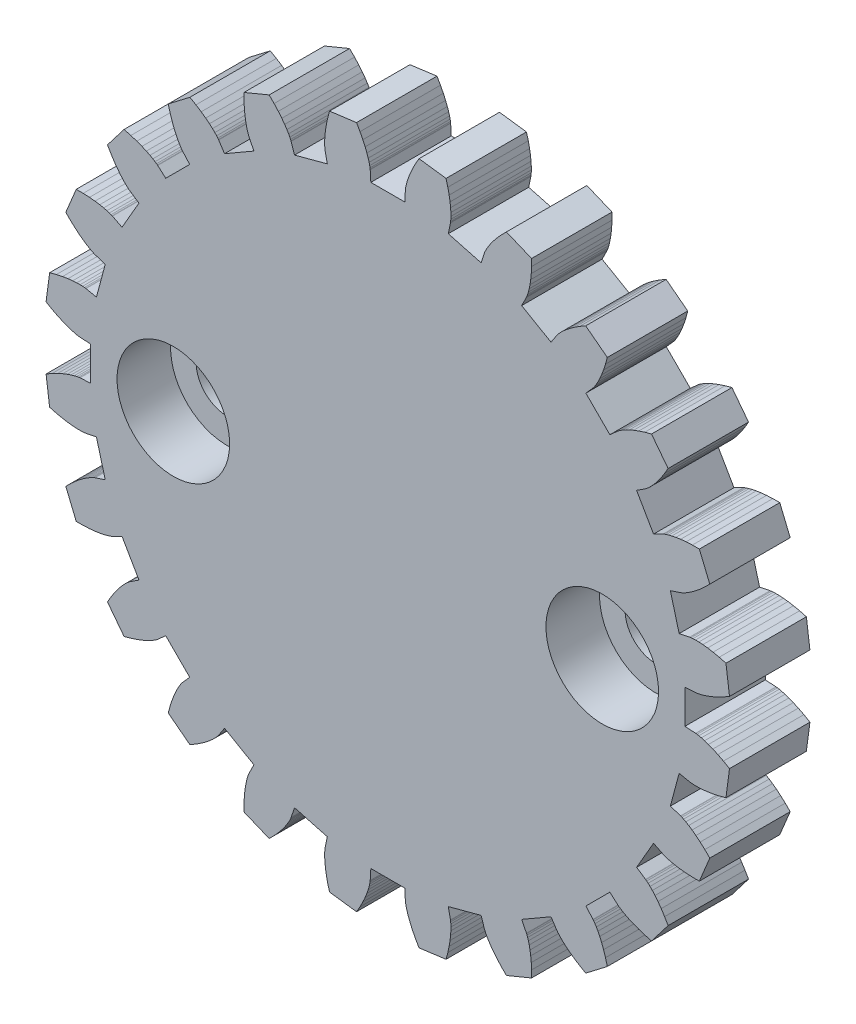
SolidWorks part; units mm, degrees
material "ABS"
ref_plane "Front Plane" through (0, 0, 0) normal (0, 0, 1) x (1, 0, 0)
ref_plane "Top Plane" through (0, 0, 0) normal (0, 1, 0) x (1, 0, 0)
ref_plane "Right Plane" through (0, 0, 0) normal (1, 0, 0) x (0, 0, -1)
sketch "Model" plane through (0, 0, 0) normal (0, 0, 1) x (1, 0, 0)
  line L0 (11.4813, -0.6559) -> (11.0819, -0.6331)
  line L1 (11.0819, -0.6331) -> (11.0819, 0.6331)
  line L2 (11.4813, 0.6559) -> (11.0819, 0.6331)
  line L3 (11.4813, 0.6559) -> (11.495, 0.6571)
  line L4 (11.495, 0.6571) -> (11.5358, 0.6626)
  line L5 (11.5358, 0.6626) -> (11.6033, 0.6749)
  line L6 (11.6033, 0.6749) -> (11.697, 0.6968)
  line L7 (11.697, 0.6968) -> (11.8158, 0.7307)
  line L8 (11.8158, 0.7307) -> (11.9589, 0.7792)
  line L9 (11.9589, 0.7792) -> (12.125, 0.8446)
  line L10 (12.125, 0.8446) -> (12.3128, 0.9294)
  line L11 (12.3128, 0.9294) -> (12.5206, 1.0358)
  line L12 (12.5206, 1.0358) -> (12.7468, 1.1658)
  line L13 (11.2598, 2.338) -> (11.2734, 2.3404)
  line L14 (11.2734, 2.3404) -> (11.3142, 2.3457)
  line L15 (11.3142, 2.3457) -> (11.3827, 2.3512)
  line L16 (11.3827, 2.3512) -> (11.4787, 2.3543)
  line L17 (11.4787, 2.3543) -> (11.6023, 2.3524)
  line L18 (11.6023, 2.3524) -> (11.7531, 2.3426)
  line L19 (11.7531, 2.3426) -> (11.9305, 2.3223)
  line L20 (11.9305, 2.3223) -> (12.1338, 2.289)
  line L21 (12.1338, 2.289) -> (12.362, 2.2401)
  line L22 (12.362, 2.2401) -> (12.6142, 2.173)
  line L23 (12.7468, 1.1658) -> (12.6142, 2.173)
  line L24 (11.2598, 2.338) -> (10.8682, 2.2567)
  line L25 (10.8682, 2.2567) -> (10.5405, 3.4797)
  line L26 (10.9203, 3.6051) -> (10.5405, 3.4797)
  line L27 (10.9203, 3.6051) -> (10.9332, 3.6098)
  line L28 (10.9332, 3.6098) -> (10.9712, 3.6257)
  line L29 (10.9712, 3.6257) -> (11.0333, 3.6551)
  line L30 (11.0333, 3.6551) -> (11.1181, 3.7004)
  line L31 (11.1181, 3.7004) -> (11.2241, 3.764)
  line L32 (11.2241, 3.764) -> (11.3497, 3.8478)
  line L33 (11.3497, 3.8478) -> (11.4933, 3.954)
  line L34 (11.4933, 3.954) -> (11.6527, 4.0845)
  line L35 (11.6527, 4.0845) -> (11.8259, 4.241)
  line L36 (11.8259, 4.241) -> (12.0107, 4.4252)
  line L37 (10.271, 5.1726) -> (10.2835, 5.1784)
  line L38 (10.2835, 5.1784) -> (10.3216, 5.1941)
  line L39 (10.3216, 5.1941) -> (10.3863, 5.2172)
  line L40 (10.3863, 5.2172) -> (10.4783, 5.245)
  line L41 (10.4783, 5.245) -> (10.5981, 5.2751)
  line L42 (10.5981, 5.2751) -> (10.7463, 5.3047)
  line L43 (10.7463, 5.3047) -> (10.9229, 5.331)
  line L44 (10.9229, 5.331) -> (11.1279, 5.3515)
  line L45 (11.1279, 5.3515) -> (11.361, 5.3633)
  line L46 (11.361, 5.3633) -> (11.622, 5.3638)
  line L47 (12.0107, 4.4252) -> (11.622, 5.3638)
  line L48 (10.271, 5.1726) -> (9.9138, 4.9927)
  line L49 (9.9138, 4.9927) -> (9.2807, 6.0892)
  line L50 (9.6151, 6.3087) -> (9.2807, 6.0892)
  line L51 (9.6151, 6.3087) -> (9.6264, 6.3166)
  line L52 (9.6264, 6.3166) -> (9.659, 6.3417)
  line L53 (9.659, 6.3417) -> (9.7113, 6.3862)
  line L54 (9.7113, 6.3862) -> (9.7815, 6.4519)
  line L55 (9.7815, 6.4519) -> (9.8675, 6.5407)
  line L56 (9.8675, 6.5407) -> (9.9671, 6.6542)
  line L57 (9.9671, 6.6542) -> (10.0783, 6.794)
  line L58 (10.0783, 6.794) -> (10.1985, 6.9613)
  line L59 (10.1985, 6.9613) -> (10.3253, 7.1573)
  line L60 (10.3253, 7.1573) -> (10.4561, 7.383)
  line L61 (8.5823, 7.6547) -> (8.5928, 7.6635)
  line L62 (8.5928, 7.6635) -> (8.6256, 7.6885)
  line L63 (8.6256, 7.6885) -> (8.6821, 7.7275)
  line L64 (8.6821, 7.7275) -> (8.7637, 7.7783)
  line L65 (8.7637, 7.7783) -> (8.8717, 7.8384)
  line L66 (8.8717, 7.8384) -> (9.0072, 7.9053)
  line L67 (9.0072, 7.9053) -> (9.1709, 7.9764)
  line L68 (9.1709, 7.9764) -> (9.3636, 8.0492)
  line L69 (9.3636, 8.0492) -> (9.5858, 8.121)
  line L70 (9.5858, 8.121) -> (9.8377, 8.189)
  line L71 (10.4561, 7.383) -> (9.8377, 8.189)
  line L72 (8.5823, 7.6547) -> (8.2838, 7.3885)
  line L73 (8.2838, 7.3885) -> (7.3885, 8.2838)
  line L74 (7.6547, 8.5823) -> (7.3885, 8.2838)
  line L75 (7.6547, 8.5823) -> (7.6635, 8.5928)
  line L76 (7.6635, 8.5928) -> (7.6885, 8.6256)
  line L77 (7.6885, 8.6256) -> (7.7275, 8.6821)
  line L78 (7.7275, 8.6821) -> (7.7783, 8.7637)
  line L79 (7.7783, 8.7637) -> (7.8384, 8.8717)
  line L80 (7.8384, 8.8717) -> (7.9053, 9.0072)
  line L81 (7.9053, 9.0072) -> (7.9764, 9.1709)
  line L82 (7.9764, 9.1709) -> (8.0492, 9.3636)
  line L83 (8.0492, 9.3636) -> (8.121, 9.5858)
  line L84 (8.121, 9.5858) -> (8.189, 9.8377)
  line L85 (6.3087, 9.6151) -> (6.3166, 9.6264)
  line L86 (6.3166, 9.6264) -> (6.3417, 9.659)
  line L87 (6.3417, 9.659) -> (6.3862, 9.7113)
  line L88 (6.3862, 9.7113) -> (6.4519, 9.7815)
  line L89 (6.4519, 9.7815) -> (6.5407, 9.8675)
  line L90 (6.5407, 9.8675) -> (6.6542, 9.9671)
  line L91 (6.6542, 9.9671) -> (6.794, 10.0783)
  line L92 (6.794, 10.0783) -> (6.9613, 10.1985)
  line L93 (6.9613, 10.1985) -> (7.1573, 10.3253)
  line L94 (7.1573, 10.3253) -> (7.383, 10.4561)
  line L95 (8.189, 9.8377) -> (7.383, 10.4561)
  line L96 (6.3087, 9.6151) -> (6.0892, 9.2807)
  line L97 (6.0892, 9.2807) -> (4.9927, 9.9138)
  line L98 (5.1726, 10.271) -> (4.9927, 9.9138)
  line L99 (5.1726, 10.271) -> (5.1784, 10.2835)
  line L100 (5.1784, 10.2835) -> (5.1941, 10.3216)
  line L101 (5.1941, 10.3216) -> (5.2172, 10.3863)
  line L102 (5.2172, 10.3863) -> (5.245, 10.4783)
  line L103 (5.245, 10.4783) -> (5.2751, 10.5981)
  line L104 (5.2751, 10.5981) -> (5.3047, 10.7463)
  line L105 (5.3047, 10.7463) -> (5.331, 10.9229)
  line L106 (5.331, 10.9229) -> (5.3515, 11.1279)
  line L107 (5.3515, 11.1279) -> (5.3633, 11.361)
  line L108 (5.3633, 11.361) -> (5.3638, 11.622)
  line L109 (3.6051, 10.9203) -> (3.6098, 10.9332)
  line L110 (3.6098, 10.9332) -> (3.6257, 10.9712)
  line L111 (3.6257, 10.9712) -> (3.6551, 11.0333)
  line L112 (3.6551, 11.0333) -> (3.7004, 11.1181)
  line L113 (3.7004, 11.1181) -> (3.764, 11.2241)
  line L114 (3.764, 11.2241) -> (3.8478, 11.3497)
  line L115 (3.8478, 11.3497) -> (3.954, 11.4933)
  line L116 (3.954, 11.4933) -> (4.0845, 11.6527)
  line L117 (4.0845, 11.6527) -> (4.241, 11.8259)
  line L118 (4.241, 11.8259) -> (4.4252, 12.0107)
  line L119 (5.3638, 11.622) -> (4.4252, 12.0107)
  line L120 (3.6051, 10.9203) -> (3.4797, 10.5405)
  line L121 (3.4797, 10.5405) -> (2.2567, 10.8682)
  line L122 (2.338, 11.2598) -> (2.2567, 10.8682)
  line L123 (2.338, 11.2598) -> (2.3404, 11.2734)
  line L124 (2.3404, 11.2734) -> (2.3457, 11.3142)
  line L125 (2.3457, 11.3142) -> (2.3512, 11.3827)
  line L126 (2.3512, 11.3827) -> (2.3543, 11.4787)
  line L127 (2.3543, 11.4787) -> (2.3524, 11.6023)
  line L128 (2.3524, 11.6023) -> (2.3426, 11.7531)
  line L129 (2.3426, 11.7531) -> (2.3223, 11.9305)
  line L130 (2.3223, 11.9305) -> (2.289, 12.1338)
  line L131 (2.289, 12.1338) -> (2.2401, 12.362)
  line L132 (2.2401, 12.362) -> (2.173, 12.6142)
  line L133 (0.6559, 11.4813) -> (0.6571, 11.495)
  line L134 (0.6571, 11.495) -> (0.6626, 11.5358)
  line L135 (0.6626, 11.5358) -> (0.6749, 11.6033)
  line L136 (0.6749, 11.6033) -> (0.6968, 11.697)
  line L137 (0.6968, 11.697) -> (0.7307, 11.8158)
  line L138 (0.7307, 11.8158) -> (0.7792, 11.9589)
  line L139 (0.7792, 11.9589) -> (0.8446, 12.125)
  line L140 (0.8446, 12.125) -> (0.9294, 12.3128)
  line L141 (0.9294, 12.3128) -> (1.0358, 12.5206)
  line L142 (1.0358, 12.5206) -> (1.1658, 12.7468)
  line L143 (2.173, 12.6142) -> (1.1658, 12.7468)
  line L144 (0.6559, 11.4813) -> (0.6331, 11.0819)
  line L145 (0.6331, 11.0819) -> (-0.6331, 11.0819)
  line L146 (-0.6559, 11.4813) -> (-0.6331, 11.0819)
  line L147 (-0.6559, 11.4813) -> (-0.6571, 11.495)
  line L148 (-0.6571, 11.495) -> (-0.6626, 11.5358)
  line L149 (-0.6626, 11.5358) -> (-0.6749, 11.6033)
  line L150 (-0.6749, 11.6033) -> (-0.6968, 11.697)
  line L151 (-0.6968, 11.697) -> (-0.7307, 11.8158)
  line L152 (-0.7307, 11.8158) -> (-0.7792, 11.9589)
  line L153 (-0.7792, 11.9589) -> (-0.8446, 12.125)
  line L154 (-0.8446, 12.125) -> (-0.9294, 12.3128)
  line L155 (-0.9294, 12.3128) -> (-1.0358, 12.5206)
  line L156 (-1.0358, 12.5206) -> (-1.1658, 12.7468)
  line L157 (-2.338, 11.2598) -> (-2.3404, 11.2734)
  line L158 (-2.3404, 11.2734) -> (-2.3457, 11.3142)
  line L159 (-2.3457, 11.3142) -> (-2.3512, 11.3827)
  line L160 (-2.3512, 11.3827) -> (-2.3543, 11.4787)
  line L161 (-2.3543, 11.4787) -> (-2.3524, 11.6023)
  line L162 (-2.3524, 11.6023) -> (-2.3426, 11.7531)
  line L163 (-2.3426, 11.7531) -> (-2.3223, 11.9305)
  line L164 (-2.3223, 11.9305) -> (-2.289, 12.1338)
  line L165 (-2.289, 12.1338) -> (-2.2401, 12.362)
  line L166 (-2.2401, 12.362) -> (-2.173, 12.6142)
  line L167 (-1.1658, 12.7468) -> (-2.173, 12.6142)
  line L168 (-2.338, 11.2598) -> (-2.2567, 10.8682)
  line L169 (-2.2567, 10.8682) -> (-3.4797, 10.5405)
  line L170 (-3.6051, 10.9203) -> (-3.4797, 10.5405)
  line L171 (-3.6051, 10.9203) -> (-3.6098, 10.9332)
  line L172 (-3.6098, 10.9332) -> (-3.6257, 10.9712)
  line L173 (-3.6257, 10.9712) -> (-3.6551, 11.0333)
  line L174 (-3.6551, 11.0333) -> (-3.7004, 11.1181)
  line L175 (-3.7004, 11.1181) -> (-3.764, 11.2241)
  line L176 (-3.764, 11.2241) -> (-3.8478, 11.3497)
  line L177 (-3.8478, 11.3497) -> (-3.954, 11.4933)
  line L178 (-3.954, 11.4933) -> (-4.0845, 11.6527)
  line L179 (-4.0845, 11.6527) -> (-4.241, 11.8259)
  line L180 (-4.241, 11.8259) -> (-4.4252, 12.0107)
  line L181 (-5.1726, 10.271) -> (-5.1784, 10.2835)
  line L182 (-5.1784, 10.2835) -> (-5.1941, 10.3216)
  line L183 (-5.1941, 10.3216) -> (-5.2172, 10.3863)
  line L184 (-5.2172, 10.3863) -> (-5.245, 10.4783)
  line L185 (-5.245, 10.4783) -> (-5.2751, 10.5981)
  line L186 (-5.2751, 10.5981) -> (-5.3047, 10.7463)
  line L187 (-5.3047, 10.7463) -> (-5.331, 10.9229)
  line L188 (-5.331, 10.9229) -> (-5.3515, 11.1279)
  line L189 (-5.3515, 11.1279) -> (-5.3633, 11.361)
  line L190 (-5.3633, 11.361) -> (-5.3638, 11.622)
  line L191 (-4.4252, 12.0107) -> (-5.3638, 11.622)
  line L192 (-5.1726, 10.271) -> (-4.9927, 9.9138)
  line L193 (-4.9927, 9.9138) -> (-6.0892, 9.2807)
  line L194 (-6.3087, 9.6151) -> (-6.0892, 9.2807)
  line L195 (-6.3087, 9.6151) -> (-6.3166, 9.6264)
  line L196 (-6.3166, 9.6264) -> (-6.3417, 9.659)
  line L197 (-6.3417, 9.659) -> (-6.3862, 9.7113)
  line L198 (-6.3862, 9.7113) -> (-6.4519, 9.7815)
  line L199 (-6.4519, 9.7815) -> (-6.5407, 9.8675)
  line L200 (-6.5407, 9.8675) -> (-6.6542, 9.9671)
  line L201 (-6.6542, 9.9671) -> (-6.794, 10.0783)
  line L202 (-6.794, 10.0783) -> (-6.9613, 10.1985)
  line L203 (-6.9613, 10.1985) -> (-7.1573, 10.3253)
  line L204 (-7.1573, 10.3253) -> (-7.383, 10.4561)
  line L205 (-7.6547, 8.5823) -> (-7.6635, 8.5928)
  line L206 (-7.6635, 8.5928) -> (-7.6885, 8.6256)
  line L207 (-7.6885, 8.6256) -> (-7.7275, 8.6821)
  line L208 (-7.7275, 8.6821) -> (-7.7783, 8.7637)
  line L209 (-7.7783, 8.7637) -> (-7.8384, 8.8717)
  line L210 (-7.8384, 8.8717) -> (-7.9053, 9.0072)
  line L211 (-7.9053, 9.0072) -> (-7.9764, 9.1709)
  line L212 (-7.9764, 9.1709) -> (-8.0492, 9.3636)
  line L213 (-8.0492, 9.3636) -> (-8.121, 9.5858)
  line L214 (-8.121, 9.5858) -> (-8.189, 9.8377)
  line L215 (-7.383, 10.4561) -> (-8.189, 9.8377)
  line L216 (-7.6547, 8.5823) -> (-7.3885, 8.2838)
  line L217 (-7.3885, 8.2838) -> (-8.2838, 7.3885)
  line L218 (-8.5823, 7.6547) -> (-8.2838, 7.3885)
  line L219 (-8.5823, 7.6547) -> (-8.5928, 7.6635)
  line L220 (-8.5928, 7.6635) -> (-8.6256, 7.6885)
  line L221 (-8.6256, 7.6885) -> (-8.6821, 7.7275)
  line L222 (-8.6821, 7.7275) -> (-8.7637, 7.7783)
  line L223 (-8.7637, 7.7783) -> (-8.8717, 7.8384)
  line L224 (-8.8717, 7.8384) -> (-9.0072, 7.9053)
  line L225 (-9.0072, 7.9053) -> (-9.1709, 7.9764)
  line L226 (-9.1709, 7.9764) -> (-9.3636, 8.0492)
  line L227 (-9.3636, 8.0492) -> (-9.5858, 8.121)
  line L228 (-9.5858, 8.121) -> (-9.8377, 8.189)
  line L229 (-9.6151, 6.3087) -> (-9.6264, 6.3166)
  line L230 (-9.6264, 6.3166) -> (-9.659, 6.3417)
  line L231 (-9.659, 6.3417) -> (-9.7113, 6.3862)
  line L232 (-9.7113, 6.3862) -> (-9.7815, 6.4519)
  line L233 (-9.7815, 6.4519) -> (-9.8675, 6.5407)
  line L234 (-9.8675, 6.5407) -> (-9.9671, 6.6542)
  line L235 (-9.9671, 6.6542) -> (-10.0783, 6.794)
  line L236 (-10.0783, 6.794) -> (-10.1985, 6.9613)
  line L237 (-10.1985, 6.9613) -> (-10.3253, 7.1573)
  line L238 (-10.3253, 7.1573) -> (-10.4561, 7.383)
  line L239 (-9.8377, 8.189) -> (-10.4561, 7.383)
  line L240 (-9.6151, 6.3087) -> (-9.2807, 6.0892)
  line L241 (-9.2807, 6.0892) -> (-9.9138, 4.9927)
  line L242 (-10.271, 5.1726) -> (-9.9138, 4.9927)
  line L243 (-10.271, 5.1726) -> (-10.2835, 5.1784)
  line L244 (-10.2835, 5.1784) -> (-10.3216, 5.1941)
  line L245 (-10.3216, 5.1941) -> (-10.3863, 5.2172)
  line L246 (-10.3863, 5.2172) -> (-10.4783, 5.245)
  line L247 (-10.4783, 5.245) -> (-10.5981, 5.2751)
  line L248 (-10.5981, 5.2751) -> (-10.7463, 5.3047)
  line L249 (-10.7463, 5.3047) -> (-10.9229, 5.331)
  line L250 (-10.9229, 5.331) -> (-11.1279, 5.3515)
  line L251 (-11.1279, 5.3515) -> (-11.361, 5.3633)
  line L252 (-11.361, 5.3633) -> (-11.622, 5.3638)
  line L253 (-10.9203, 3.6051) -> (-10.9332, 3.6098)
  line L254 (-10.9332, 3.6098) -> (-10.9712, 3.6257)
  line L255 (-10.9712, 3.6257) -> (-11.0333, 3.6551)
  line L256 (-11.0333, 3.6551) -> (-11.1181, 3.7004)
  line L257 (-11.1181, 3.7004) -> (-11.2241, 3.764)
  line L258 (-11.2241, 3.764) -> (-11.3497, 3.8478)
  line L259 (-11.3497, 3.8478) -> (-11.4933, 3.954)
  line L260 (-11.4933, 3.954) -> (-11.6527, 4.0845)
  line L261 (-11.6527, 4.0845) -> (-11.8259, 4.241)
  line L262 (-11.8259, 4.241) -> (-12.0107, 4.4252)
  line L263 (-11.622, 5.3638) -> (-12.0107, 4.4252)
  line L264 (-10.9203, 3.6051) -> (-10.5405, 3.4797)
  line L265 (-10.5405, 3.4797) -> (-10.8682, 2.2567)
  line L266 (-11.2598, 2.338) -> (-10.8682, 2.2567)
  line L267 (-11.2598, 2.338) -> (-11.2734, 2.3404)
  line L268 (-11.2734, 2.3404) -> (-11.3142, 2.3457)
  line L269 (-11.3142, 2.3457) -> (-11.3827, 2.3512)
  line L270 (-11.3827, 2.3512) -> (-11.4787, 2.3543)
  line L271 (-11.4787, 2.3543) -> (-11.6023, 2.3524)
  line L272 (-11.6023, 2.3524) -> (-11.7531, 2.3426)
  line L273 (-11.7531, 2.3426) -> (-11.9305, 2.3223)
  line L274 (-11.9305, 2.3223) -> (-12.1338, 2.289)
  line L275 (-12.1338, 2.289) -> (-12.362, 2.2401)
  line L276 (-12.362, 2.2401) -> (-12.6142, 2.173)
  line L277 (-11.4813, 0.6559) -> (-11.495, 0.6571)
  line L278 (-11.495, 0.6571) -> (-11.5358, 0.6626)
  line L279 (-11.5358, 0.6626) -> (-11.6033, 0.6749)
  line L280 (-11.6033, 0.6749) -> (-11.697, 0.6968)
  line L281 (-11.697, 0.6968) -> (-11.8158, 0.7307)
  line L282 (-11.8158, 0.7307) -> (-11.9589, 0.7792)
  line L283 (-11.9589, 0.7792) -> (-12.125, 0.8446)
  line L284 (-12.125, 0.8446) -> (-12.3128, 0.9294)
  line L285 (-12.3128, 0.9294) -> (-12.5206, 1.0358)
  line L286 (-12.5206, 1.0358) -> (-12.7468, 1.1658)
  line L287 (-12.6142, 2.173) -> (-12.7468, 1.1658)
  line L288 (-11.4813, 0.6559) -> (-11.0819, 0.6331)
  line L289 (-11.0819, 0.6331) -> (-11.0819, -0.6331)
  line L290 (-11.4813, -0.6559) -> (-11.0819, -0.6331)
  line L291 (-11.4813, -0.6559) -> (-11.495, -0.6571)
  line L292 (-11.495, -0.6571) -> (-11.5358, -0.6626)
  line L293 (-11.5358, -0.6626) -> (-11.6033, -0.6749)
  line L294 (-11.6033, -0.6749) -> (-11.697, -0.6968)
  line L295 (-11.697, -0.6968) -> (-11.8158, -0.7307)
  line L296 (-11.8158, -0.7307) -> (-11.9589, -0.7792)
  line L297 (-11.9589, -0.7792) -> (-12.125, -0.8446)
  line L298 (-12.125, -0.8446) -> (-12.3128, -0.9294)
  line L299 (-12.3128, -0.9294) -> (-12.5206, -1.0358)
  line L300 (-12.5206, -1.0358) -> (-12.7468, -1.1658)
  line L301 (-11.2598, -2.338) -> (-11.2734, -2.3404)
  line L302 (-11.2734, -2.3404) -> (-11.3142, -2.3457)
  line L303 (-11.3142, -2.3457) -> (-11.3827, -2.3512)
  line L304 (-11.3827, -2.3512) -> (-11.4787, -2.3543)
  line L305 (-11.4787, -2.3543) -> (-11.6023, -2.3524)
  line L306 (-11.6023, -2.3524) -> (-11.7531, -2.3426)
  line L307 (-11.7531, -2.3426) -> (-11.9305, -2.3223)
  line L308 (-11.9305, -2.3223) -> (-12.1338, -2.289)
  line L309 (-12.1338, -2.289) -> (-12.362, -2.2401)
  line L310 (-12.362, -2.2401) -> (-12.6142, -2.173)
  line L311 (-12.7468, -1.1658) -> (-12.6142, -2.173)
  line L312 (-11.2598, -2.338) -> (-10.8682, -2.2567)
  line L313 (-10.8682, -2.2567) -> (-10.5405, -3.4797)
  line L314 (-10.9203, -3.6051) -> (-10.5405, -3.4797)
  line L315 (-10.9203, -3.6051) -> (-10.9332, -3.6098)
  line L316 (-10.9332, -3.6098) -> (-10.9712, -3.6257)
  line L317 (-10.9712, -3.6257) -> (-11.0333, -3.6551)
  line L318 (-11.0333, -3.6551) -> (-11.1181, -3.7004)
  line L319 (-11.1181, -3.7004) -> (-11.2241, -3.764)
  line L320 (-11.2241, -3.764) -> (-11.3497, -3.8478)
  line L321 (-11.3497, -3.8478) -> (-11.4933, -3.954)
  line L322 (-11.4933, -3.954) -> (-11.6527, -4.0845)
  line L323 (-11.6527, -4.0845) -> (-11.8259, -4.241)
  line L324 (-11.8259, -4.241) -> (-12.0107, -4.4252)
  line L325 (-10.271, -5.1726) -> (-10.2835, -5.1784)
  line L326 (-10.2835, -5.1784) -> (-10.3216, -5.1941)
  line L327 (-10.3216, -5.1941) -> (-10.3863, -5.2172)
  line L328 (-10.3863, -5.2172) -> (-10.4783, -5.245)
  line L329 (-10.4783, -5.245) -> (-10.5981, -5.2751)
  line L330 (-10.5981, -5.2751) -> (-10.7463, -5.3047)
  line L331 (-10.7463, -5.3047) -> (-10.9229, -5.331)
  line L332 (-10.9229, -5.331) -> (-11.1279, -5.3515)
  line L333 (-11.1279, -5.3515) -> (-11.361, -5.3633)
  line L334 (-11.361, -5.3633) -> (-11.622, -5.3638)
  line L335 (-12.0107, -4.4252) -> (-11.622, -5.3638)
  line L336 (-10.271, -5.1726) -> (-9.9138, -4.9927)
  line L337 (-9.9138, -4.9927) -> (-9.2807, -6.0892)
  line L338 (-9.6151, -6.3087) -> (-9.2807, -6.0892)
  line L339 (-9.6151, -6.3087) -> (-9.6264, -6.3166)
  line L340 (-9.6264, -6.3166) -> (-9.659, -6.3417)
  line L341 (-9.659, -6.3417) -> (-9.7113, -6.3862)
  line L342 (-9.7113, -6.3862) -> (-9.7815, -6.4519)
  line L343 (-9.7815, -6.4519) -> (-9.8675, -6.5407)
  line L344 (-9.8675, -6.5407) -> (-9.9671, -6.6542)
  line L345 (-9.9671, -6.6542) -> (-10.0783, -6.794)
  line L346 (-10.0783, -6.794) -> (-10.1985, -6.9613)
  line L347 (-10.1985, -6.9613) -> (-10.3253, -7.1573)
  line L348 (-10.3253, -7.1573) -> (-10.4561, -7.383)
  line L349 (-8.5823, -7.6547) -> (-8.5928, -7.6635)
  line L350 (-8.5928, -7.6635) -> (-8.6256, -7.6885)
  line L351 (-8.6256, -7.6885) -> (-8.6821, -7.7275)
  line L352 (-8.6821, -7.7275) -> (-8.7637, -7.7783)
  line L353 (-8.7637, -7.7783) -> (-8.8717, -7.8384)
  line L354 (-8.8717, -7.8384) -> (-9.0072, -7.9053)
  line L355 (-9.0072, -7.9053) -> (-9.1709, -7.9764)
  line L356 (-9.1709, -7.9764) -> (-9.3636, -8.0492)
  line L357 (-9.3636, -8.0492) -> (-9.5858, -8.121)
  line L358 (-9.5858, -8.121) -> (-9.8377, -8.189)
  line L359 (-10.4561, -7.383) -> (-9.8377, -8.189)
  line L360 (-8.5823, -7.6547) -> (-8.2838, -7.3885)
  line L361 (-8.2838, -7.3885) -> (-7.3885, -8.2838)
  line L362 (-7.6547, -8.5823) -> (-7.3885, -8.2838)
  line L363 (-7.6547, -8.5823) -> (-7.6635, -8.5928)
  line L364 (-7.6635, -8.5928) -> (-7.6885, -8.6256)
  line L365 (-7.6885, -8.6256) -> (-7.7275, -8.6821)
  line L366 (-7.7275, -8.6821) -> (-7.7783, -8.7637)
  line L367 (-7.7783, -8.7637) -> (-7.8384, -8.8717)
  line L368 (-7.8384, -8.8717) -> (-7.9053, -9.0072)
  line L369 (-7.9053, -9.0072) -> (-7.9764, -9.1709)
  line L370 (-7.9764, -9.1709) -> (-8.0492, -9.3636)
  line L371 (-8.0492, -9.3636) -> (-8.121, -9.5858)
  line L372 (-8.121, -9.5858) -> (-8.189, -9.8377)
  line L373 (-6.3087, -9.6151) -> (-6.3166, -9.6264)
  line L374 (-6.3166, -9.6264) -> (-6.3417, -9.659)
  line L375 (-6.3417, -9.659) -> (-6.3862, -9.7113)
  line L376 (-6.3862, -9.7113) -> (-6.4519, -9.7815)
  line L377 (-6.4519, -9.7815) -> (-6.5407, -9.8675)
  line L378 (-6.5407, -9.8675) -> (-6.6542, -9.9671)
  line L379 (-6.6542, -9.9671) -> (-6.794, -10.0783)
  line L380 (-6.794, -10.0783) -> (-6.9613, -10.1985)
  line L381 (-6.9613, -10.1985) -> (-7.1573, -10.3253)
  line L382 (-7.1573, -10.3253) -> (-7.383, -10.4561)
  line L383 (-8.189, -9.8377) -> (-7.383, -10.4561)
  line L384 (-6.3087, -9.6151) -> (-6.0892, -9.2807)
  line L385 (-6.0892, -9.2807) -> (-4.9927, -9.9138)
  line L386 (-5.1726, -10.271) -> (-4.9927, -9.9138)
  line L387 (-5.1726, -10.271) -> (-5.1784, -10.2835)
  line L388 (-5.1784, -10.2835) -> (-5.1941, -10.3216)
  line L389 (-5.1941, -10.3216) -> (-5.2172, -10.3863)
  line L390 (-5.2172, -10.3863) -> (-5.245, -10.4783)
  line L391 (-5.245, -10.4783) -> (-5.2751, -10.5981)
  line L392 (-5.2751, -10.5981) -> (-5.3047, -10.7463)
  line L393 (-5.3047, -10.7463) -> (-5.331, -10.9229)
  line L394 (-5.331, -10.9229) -> (-5.3515, -11.1279)
  line L395 (-5.3515, -11.1279) -> (-5.3633, -11.361)
  line L396 (-5.3633, -11.361) -> (-5.3638, -11.622)
  line L397 (-3.6051, -10.9203) -> (-3.6098, -10.9332)
  line L398 (-3.6098, -10.9332) -> (-3.6257, -10.9712)
  line L399 (-3.6257, -10.9712) -> (-3.6551, -11.0333)
  line L400 (-3.6551, -11.0333) -> (-3.7004, -11.1181)
  line L401 (-3.7004, -11.1181) -> (-3.764, -11.2241)
  line L402 (-3.764, -11.2241) -> (-3.8478, -11.3497)
  line L403 (-3.8478, -11.3497) -> (-3.954, -11.4933)
  line L404 (-3.954, -11.4933) -> (-4.0845, -11.6527)
  line L405 (-4.0845, -11.6527) -> (-4.241, -11.8259)
  line L406 (-4.241, -11.8259) -> (-4.4252, -12.0107)
  line L407 (-5.3638, -11.622) -> (-4.4252, -12.0107)
  line L408 (-3.6051, -10.9203) -> (-3.4797, -10.5405)
  line L409 (-3.4797, -10.5405) -> (-2.2567, -10.8682)
  line L410 (-2.338, -11.2598) -> (-2.2567, -10.8682)
  line L411 (-2.338, -11.2598) -> (-2.3404, -11.2734)
  line L412 (-2.3404, -11.2734) -> (-2.3457, -11.3142)
  line L413 (-2.3457, -11.3142) -> (-2.3512, -11.3827)
  line L414 (-2.3512, -11.3827) -> (-2.3543, -11.4787)
  line L415 (-2.3543, -11.4787) -> (-2.3524, -11.6023)
  line L416 (-2.3524, -11.6023) -> (-2.3426, -11.7531)
  line L417 (-2.3426, -11.7531) -> (-2.3223, -11.9305)
  line L418 (-2.3223, -11.9305) -> (-2.289, -12.1338)
  line L419 (-2.289, -12.1338) -> (-2.2401, -12.362)
  line L420 (-2.2401, -12.362) -> (-2.173, -12.6142)
  line L421 (-0.6559, -11.4813) -> (-0.6571, -11.495)
  line L422 (-0.6571, -11.495) -> (-0.6626, -11.5358)
  line L423 (-0.6626, -11.5358) -> (-0.6749, -11.6033)
  line L424 (-0.6749, -11.6033) -> (-0.6968, -11.697)
  line L425 (-0.6968, -11.697) -> (-0.7307, -11.8158)
  line L426 (-0.7307, -11.8158) -> (-0.7792, -11.9589)
  line L427 (-0.7792, -11.9589) -> (-0.8446, -12.125)
  line L428 (-0.8446, -12.125) -> (-0.9294, -12.3128)
  line L429 (-0.9294, -12.3128) -> (-1.0358, -12.5206)
  line L430 (-1.0358, -12.5206) -> (-1.1658, -12.7468)
  line L431 (-2.173, -12.6142) -> (-1.1658, -12.7468)
  line L432 (-0.6559, -11.4813) -> (-0.6331, -11.0819)
  line L433 (-0.6331, -11.0819) -> (0.6331, -11.0819)
  line L434 (0.6559, -11.4813) -> (0.6331, -11.0819)
  line L435 (0.6559, -11.4813) -> (0.6571, -11.495)
  line L436 (0.6571, -11.495) -> (0.6626, -11.5358)
  line L437 (0.6626, -11.5358) -> (0.6749, -11.6033)
  line L438 (0.6749, -11.6033) -> (0.6968, -11.697)
  line L439 (0.6968, -11.697) -> (0.7307, -11.8158)
  line L440 (0.7307, -11.8158) -> (0.7792, -11.9589)
  line L441 (0.7792, -11.9589) -> (0.8446, -12.125)
  line L442 (0.8446, -12.125) -> (0.9294, -12.3128)
  line L443 (0.9294, -12.3128) -> (1.0358, -12.5206)
  line L444 (1.0358, -12.5206) -> (1.1658, -12.7468)
  line L445 (2.338, -11.2598) -> (2.3404, -11.2734)
  line L446 (2.3404, -11.2734) -> (2.3457, -11.3142)
  line L447 (2.3457, -11.3142) -> (2.3512, -11.3827)
  line L448 (2.3512, -11.3827) -> (2.3543, -11.4787)
  line L449 (2.3543, -11.4787) -> (2.3524, -11.6023)
  line L450 (2.3524, -11.6023) -> (2.3426, -11.7531)
  line L451 (2.3426, -11.7531) -> (2.3223, -11.9305)
  line L452 (2.3223, -11.9305) -> (2.289, -12.1338)
  line L453 (2.289, -12.1338) -> (2.2401, -12.362)
  line L454 (2.2401, -12.362) -> (2.173, -12.6142)
  line L455 (1.1658, -12.7468) -> (2.173, -12.6142)
  line L456 (2.338, -11.2598) -> (2.2567, -10.8682)
  line L457 (2.2567, -10.8682) -> (3.4797, -10.5405)
  line L458 (3.6051, -10.9203) -> (3.4797, -10.5405)
  line L459 (3.6051, -10.9203) -> (3.6098, -10.9332)
  line L460 (3.6098, -10.9332) -> (3.6257, -10.9712)
  line L461 (3.6257, -10.9712) -> (3.6551, -11.0333)
  line L462 (3.6551, -11.0333) -> (3.7004, -11.1181)
  line L463 (3.7004, -11.1181) -> (3.764, -11.2241)
  line L464 (3.764, -11.2241) -> (3.8478, -11.3497)
  line L465 (3.8478, -11.3497) -> (3.954, -11.4933)
  line L466 (3.954, -11.4933) -> (4.0845, -11.6527)
  line L467 (4.0845, -11.6527) -> (4.241, -11.8259)
  line L468 (4.241, -11.8259) -> (4.4252, -12.0107)
  line L469 (5.1726, -10.271) -> (5.1784, -10.2835)
  line L470 (5.1784, -10.2835) -> (5.1941, -10.3216)
  line L471 (5.1941, -10.3216) -> (5.2172, -10.3863)
  line L472 (5.2172, -10.3863) -> (5.245, -10.4783)
  line L473 (5.245, -10.4783) -> (5.2751, -10.5981)
  line L474 (5.2751, -10.5981) -> (5.3047, -10.7463)
  line L475 (5.3047, -10.7463) -> (5.331, -10.9229)
  line L476 (5.331, -10.9229) -> (5.3515, -11.1279)
  line L477 (5.3515, -11.1279) -> (5.3633, -11.361)
  line L478 (5.3633, -11.361) -> (5.3638, -11.622)
  line L479 (4.4252, -12.0107) -> (5.3638, -11.622)
  line L480 (5.1726, -10.271) -> (4.9927, -9.9138)
  line L481 (4.9927, -9.9138) -> (6.0892, -9.2807)
  line L482 (6.3087, -9.6151) -> (6.0892, -9.2807)
  line L483 (6.3087, -9.6151) -> (6.3166, -9.6264)
  line L484 (6.3166, -9.6264) -> (6.3417, -9.659)
  line L485 (6.3417, -9.659) -> (6.3862, -9.7113)
  line L486 (6.3862, -9.7113) -> (6.4519, -9.7815)
  line L487 (6.4519, -9.7815) -> (6.5407, -9.8675)
  line L488 (6.5407, -9.8675) -> (6.6542, -9.9671)
  line L489 (6.6542, -9.9671) -> (6.794, -10.0783)
  line L490 (6.794, -10.0783) -> (6.9613, -10.1985)
  line L491 (6.9613, -10.1985) -> (7.1573, -10.3253)
  line L492 (7.1573, -10.3253) -> (7.383, -10.4561)
  line L493 (7.6547, -8.5823) -> (7.6635, -8.5928)
  line L494 (7.6635, -8.5928) -> (7.6885, -8.6256)
  line L495 (7.6885, -8.6256) -> (7.7275, -8.6821)
  line L496 (7.7275, -8.6821) -> (7.7783, -8.7637)
  line L497 (7.7783, -8.7637) -> (7.8384, -8.8717)
  line L498 (7.8384, -8.8717) -> (7.9053, -9.0072)
  line L499 (7.9053, -9.0072) -> (7.9764, -9.1709)
  line L500 (7.9764, -9.1709) -> (8.0492, -9.3636)
  line L501 (8.0492, -9.3636) -> (8.121, -9.5858)
  line L502 (8.121, -9.5858) -> (8.189, -9.8377)
  line L503 (7.383, -10.4561) -> (8.189, -9.8377)
  line L504 (7.6547, -8.5823) -> (7.3885, -8.2838)
  line L505 (7.3885, -8.2838) -> (8.2838, -7.3885)
  line L506 (8.5823, -7.6547) -> (8.2838, -7.3885)
  line L507 (8.5823, -7.6547) -> (8.5928, -7.6635)
  line L508 (8.5928, -7.6635) -> (8.6256, -7.6885)
  line L509 (8.6256, -7.6885) -> (8.6821, -7.7275)
  line L510 (8.6821, -7.7275) -> (8.7637, -7.7783)
  line L511 (8.7637, -7.7783) -> (8.8717, -7.8384)
  line L512 (8.8717, -7.8384) -> (9.0072, -7.9053)
  line L513 (9.0072, -7.9053) -> (9.1709, -7.9764)
  line L514 (9.1709, -7.9764) -> (9.3636, -8.0492)
  line L515 (9.3636, -8.0492) -> (9.5858, -8.121)
  line L516 (9.5858, -8.121) -> (9.8377, -8.189)
  line L517 (9.6151, -6.3087) -> (9.6264, -6.3166)
  line L518 (9.6264, -6.3166) -> (9.659, -6.3417)
  line L519 (9.659, -6.3417) -> (9.7113, -6.3862)
  line L520 (9.7113, -6.3862) -> (9.7815, -6.4519)
  line L521 (9.7815, -6.4519) -> (9.8675, -6.5407)
  line L522 (9.8675, -6.5407) -> (9.9671, -6.6542)
  line L523 (9.9671, -6.6542) -> (10.0783, -6.794)
  line L524 (10.0783, -6.794) -> (10.1985, -6.9613)
  line L525 (10.1985, -6.9613) -> (10.3253, -7.1573)
  line L526 (10.3253, -7.1573) -> (10.4561, -7.383)
  line L527 (9.8377, -8.189) -> (10.4561, -7.383)
  line L528 (9.6151, -6.3087) -> (9.2807, -6.0892)
  line L529 (9.2807, -6.0892) -> (9.9138, -4.9927)
  line L530 (10.271, -5.1726) -> (9.9138, -4.9927)
  line L531 (10.271, -5.1726) -> (10.2835, -5.1784)
  line L532 (10.2835, -5.1784) -> (10.3216, -5.1941)
  line L533 (10.3216, -5.1941) -> (10.3863, -5.2172)
  line L534 (10.3863, -5.2172) -> (10.4783, -5.245)
  line L535 (10.4783, -5.245) -> (10.5981, -5.2751)
  line L536 (10.5981, -5.2751) -> (10.7463, -5.3047)
  line L537 (10.7463, -5.3047) -> (10.9229, -5.331)
  line L538 (10.9229, -5.331) -> (11.1279, -5.3515)
  line L539 (11.1279, -5.3515) -> (11.361, -5.3633)
  line L540 (11.361, -5.3633) -> (11.622, -5.3638)
  line L541 (10.9203, -3.6051) -> (10.9332, -3.6098)
  line L542 (10.9332, -3.6098) -> (10.9712, -3.6257)
  line L543 (10.9712, -3.6257) -> (11.0333, -3.6551)
  line L544 (11.0333, -3.6551) -> (11.1181, -3.7004)
  line L545 (11.1181, -3.7004) -> (11.2241, -3.764)
  line L546 (11.2241, -3.764) -> (11.3497, -3.8478)
  line L547 (11.3497, -3.8478) -> (11.4933, -3.954)
  line L548 (11.4933, -3.954) -> (11.6527, -4.0845)
  line L549 (11.6527, -4.0845) -> (11.8259, -4.241)
  line L550 (11.8259, -4.241) -> (12.0107, -4.4252)
  line L551 (11.622, -5.3638) -> (12.0107, -4.4252)
  line L552 (10.9203, -3.6051) -> (10.5405, -3.4797)
  line L553 (10.5405, -3.4797) -> (10.8682, -2.2567)
  line L554 (11.2598, -2.338) -> (10.8682, -2.2567)
  line L555 (11.2598, -2.338) -> (11.2734, -2.3404)
  line L556 (11.2734, -2.3404) -> (11.3142, -2.3457)
  line L557 (11.3142, -2.3457) -> (11.3827, -2.3512)
  line L558 (11.3827, -2.3512) -> (11.4787, -2.3543)
  line L559 (11.4787, -2.3543) -> (11.6023, -2.3524)
  line L560 (11.6023, -2.3524) -> (11.7531, -2.3426)
  line L561 (11.7531, -2.3426) -> (11.9305, -2.3223)
  line L562 (11.9305, -2.3223) -> (12.1338, -2.289)
  line L563 (12.1338, -2.289) -> (12.362, -2.2401)
  line L564 (12.362, -2.2401) -> (12.6142, -2.173)
  line L565 (11.4813, -0.6559) -> (11.495, -0.6571)
  line L566 (11.495, -0.6571) -> (11.5358, -0.6626)
  line L567 (11.5358, -0.6626) -> (11.6033, -0.6749)
  line L568 (11.6033, -0.6749) -> (11.697, -0.6968)
  line L569 (11.697, -0.6968) -> (11.8158, -0.7307)
  line L570 (11.8158, -0.7307) -> (11.9589, -0.7792)
  line L571 (11.9589, -0.7792) -> (12.125, -0.8446)
  line L572 (12.125, -0.8446) -> (12.3128, -0.9294)
  line L573 (12.3128, -0.9294) -> (12.5206, -1.0358)
  line L574 (12.5206, -1.0358) -> (12.7468, -1.1658)
  line L575 (12.6142, -2.173) -> (12.7468, -1.1658)
extrude "Main Gear Body" add sketch "Model" along normal blind 3
sketch "Sketch1" plane through (0, 0, 3) normal (0, 0, 1) x (1, 0, 0)
  line L0 (-8, 0) -> (8, 0) construction
  circle A0 centre (0, 0) radius 4.075
  circle A1 centre (-8, 0) radius 1.15
  circle A2 centre (8, 0) radius 1.15
  dimension "D1" = 16
  dimension "D2" = 2.3
  dimension "D3" = 8.15
extrude "Servo Clearance" cut sketch "Sketch1" against normal through all
sketch "Sketch2" plane through (0, 0, 3) normal (0, 0, 1) x (1, 0, 0)
  circle A0 centre (8, 0) radius 2.1
  circle A1 centre (-8, 0) radius 2.1
  circle A3 centre (-8, 0) radius 1.15 construction
  circle A4 centre (8, 0) radius 1.15 construction
  dimension "D1" = 4.2
extrude "Bolt Head Clearance" cut sketch "Sketch2" against normal blind 2
ref_point "Point1"
sketch "Sketch4" plane through (0, 0, 3) normal (0, 0, 1) x (1, 0, 0)
  circle A0 centre (0, 0) radius 4.075
extrude "Boss-Extrude2" add sketch "Sketch4" against normal blind 1
